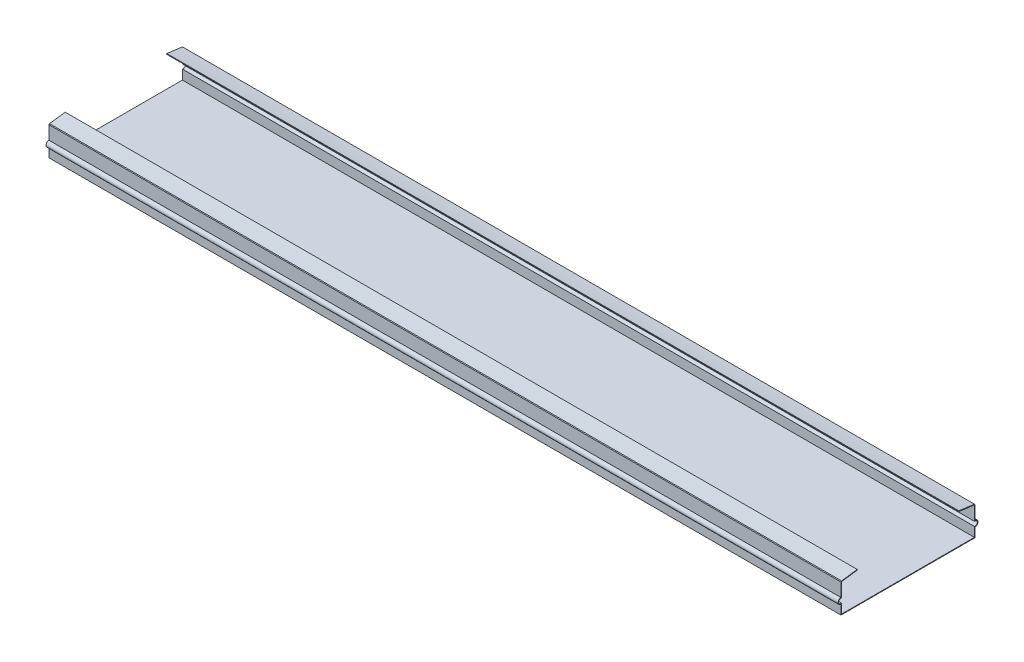
SolidWorks part; units mm, degrees
ref_plane "Front Plane" through (0, 0, 0) normal (0, 0, 1) x (1, 0, 0)
ref_plane "Top Plane" through (0, 0, 0) normal (0, 1, 0) x (1, 0, 0)
ref_plane "Right Plane" through (0, 0, 0) normal (1, 0, 0) x (0, 0, -1)
sketch "Sketch1" plane through (0, 0, 0) normal (0, 1, 0) x (1, 0, 0)
  line L0 (0, 21.5) -> (0, -21.5) construction
  line L1 (-133.0182, 21.5) -> (120.9818, 21.5)
  line L2 (-133.0182, 21.5) -> (-133.0182, -21.5)
  line L3 (-133.0182, -21.5) -> (120.9818, -21.5)
  line L4 (120.9818, 21.5) -> (120.9818, -21.5)
  dimension "D1" = 254
  dimension "D2" = 43
extrude "Boss-Extrude1" add sketch "Sketch1" along normal blind 0.2
sketch "Sketch2" plane through (0, 0.2, 0) normal (0, 1, 0) x (1, 0, 0)
  line L0 (120.9818, 21.5) -> (-133.0182, 21.5) construction
  line L1 (120.9818, 21.5) -> (-133.0182, 21.5)
ref_plane "Plane1" through (-133.0182, 0, 0) normal (1, 0, 0) x (0, 0, -1)
sketch "Sketch4" plane through (-133.0182, 0, 0) normal (1, 0, 0) x (0, 0, -1)
  line L0 (21.5, 0.2) -> (21.5, 3.0056)
  line L1 (21.5, 4.8842) -> (21.5, 9.2)
  line L3 (21.2968, 0.2) -> (21.2968, 3.2374)
  line L4 (21.2968, 4.6524) -> (21.2968, 9.2)
  line L5 (21.2968, 0.2) -> (21.5, 0.2)
  line L7 (16.2805, 10.0751) -> (16.247, 9.8747)
  line L8 (21.3171, 9.4022) -> (21.5, 9.2)
  arc A0 (21.5, 3.0056) -> (21.5, 4.8842) centre (21.5, 3.9449) ccw
  arc A1 (21.2968, 3.2374) -> (21.2968, 4.6524) centre (21.5, 3.9449) ccw
  spline S0 degree 2 poles (21.2968, 9.2) (18.76, 9.455) (16.247, 9.8747) knots 0 0 0 1 1 1
  spline S1 degree 1 poles (21.3171, 9.4022) (16.2805, 10.0751) knots 0 0 1 1 construction
  spline S2 degree 3 poles (21.3171, 9.4022) (19.6318, 9.5716) (17.9511, 9.7961) (16.2805, 10.0751) knots 0 0 0 0 1 1 1 1
  dimension "D1" = 9
  dimension "D2" = 0.2032
  dimension "D3" = 0.2032
extrude "Boss-Extrude2" add sketch "Sketch4" along normal blind 254
mirror "Mirror1" about plane through (0, 0, 0) normal (0, 0, 1) of "Boss-Extrude2"
